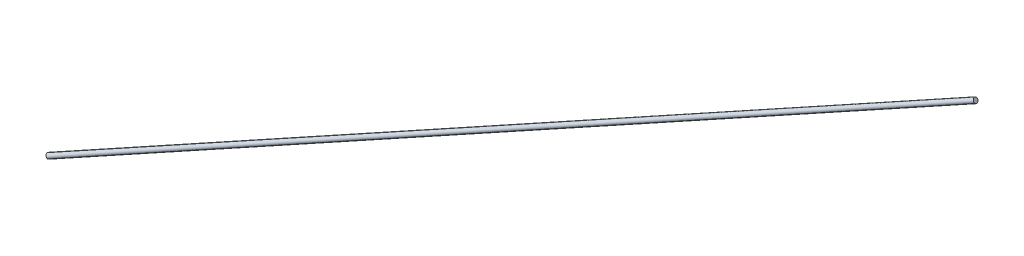
SolidWorks part; units mm, degrees
ref_plane "Front Plane" through (0, 0, 0) normal (0, 0, 1) x (1, 0, 0)
ref_plane "Top Plane" through (0, 0, 0) normal (0, 1, 0) x (1, 0, 0)
ref_plane "Right Plane" through (0, 0, 0) normal (1, 0, 0) x (0, 0, -1)
sketch3d "3DSketch1"
  line L0 (1158.9508, 2608.9171, 1146.6546) -> (1158.9508, 2608.9171, 1451.4546) construction
  line L1 (1158.9508, 2608.9171, 1146.6546) -> (1158.9508, 2608.9171, 1756.2546) construction
  line L2 (1158.9508, 2608.9171, 1451.4546) -> (1158.9508, 2603.8371, 1451.4546) construction
  line L3 (-479.3492, 1821.5171, 1756.2546) -> (-479.3492, 1821.5171, 1761.3346) construction
  line L4 (-479.3492, 1821.5171, 1146.6546) -> (-479.3492, 1821.5171, 1141.5746) construction
  line L5 (1158.9508, 2603.8371, 1413.3546) -> (1158.9508, 2603.8371, 1489.5546) construction
  line L6 (-479.3492, 1821.5171, 1141.5746) -> (1158.9508, 2603.8371, 1413.3546) construction
  line L7 (1158.9508, 2603.8371, 1489.5546) -> (-479.3492, 1821.5171, 1761.3346)
  point P14 (1158.9508, 2603.8371, 1451.4546)
  dimension "D1" = 5.08
  dimension "D2" = 5.08
  dimension "D3" = 5.08
  dimension "D4" = 76.2
sweep "Sweep1" add path "3DSketch1" circular profile diameter 10.16 parameters "D3"=10.16
